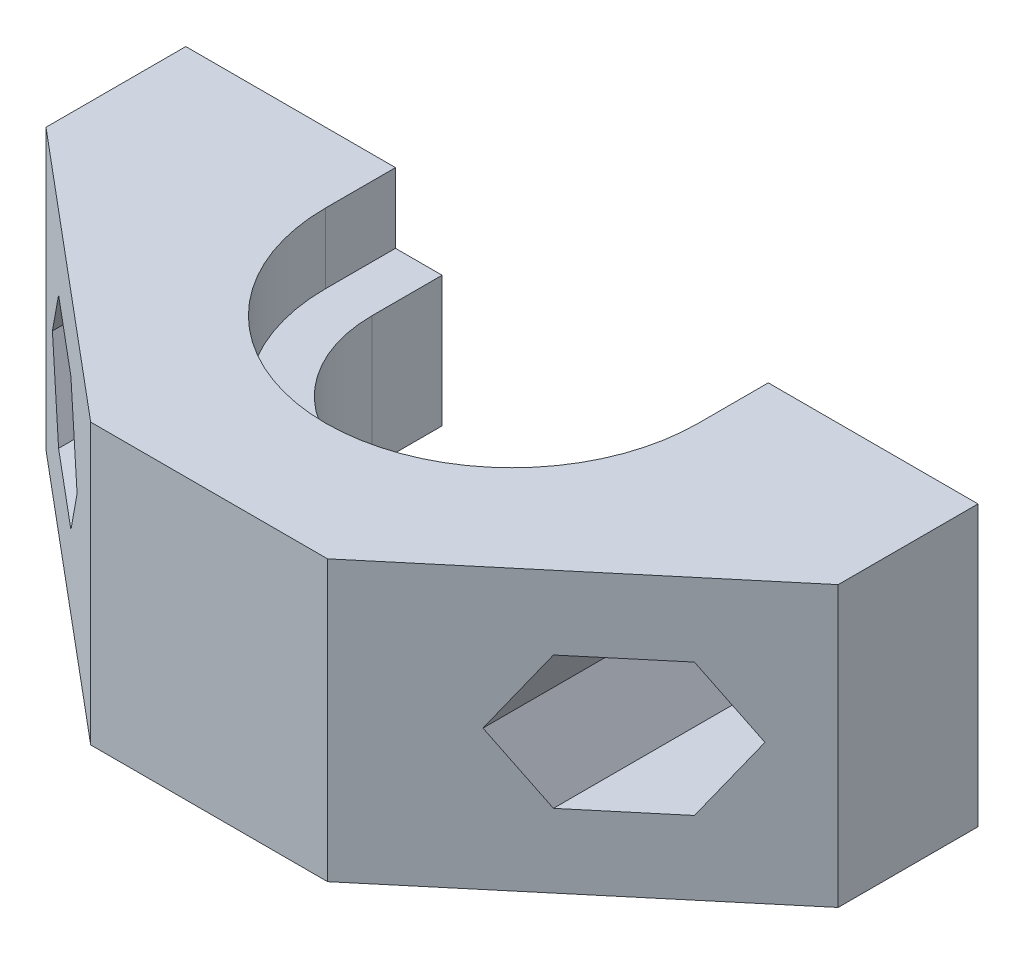
SolidWorks part; units mm, degrees
ref_plane "前视基准面" through (0, 0, 0) normal (0, 0, 1) x (1, 0, 0)
ref_plane "上视基准面" through (0, 0, 0) normal (0, 1, 0) x (1, 0, 0)
ref_plane "右视基准面" through (0, 0, 0) normal (1, 0, 0) x (0, 0, -1)
sketch "草图1" plane through (0, 0, 0) normal (0, 1, 0) x (1, 0, 0)
  line L2 (-17, -3) -> (-5.0825, -13)
  line L3 (-5.0825, -13) -> (5.0825, -13)
  line L4 (5.0825, -13) -> (17, -3)
  line L5 (17, -3) -> (17, 0)
  line L6 (0, 0) -> (0, 11.7213) construction
  line L7 (8, 0) -> (7.9845, 0)
  line L9 (-17, 3) -> (-8, 3)
  line L10 (-8, 3) -> (-8, 0)
  line L12 (17, 0) -> (17, 3)
  line L13 (17, 3) -> (7.9845, 3)
  line L14 (7.9845, 3) -> (7.9845, 0)
  line L17 (0, 0) -> (-32.6712, 0) construction
  line L18 (-17, -3) -> (-17, 3)
  arc A0 (-8, 0) -> (8, 0) centre (0, 0) ccw
  dimension "D1" = 16
  dimension "D2" = 3
  dimension "D3" = 17
  dimension "D4" = 3
  dimension "D5" = 17
  dimension "D7" = 140
  dimension "D8" = 140
  dimension "D11" = 3
extrude "凸台-拉伸1" add sketch "草图1" along normal blind 3.4
sketch "草图2" plane through (0, 3.4, 0) normal (0, 1, 0) x (1, 0, 0)
  line L8 (-8, 0) -> (-8, 3)
  line L9 (-17, -3) -> (-5.0825, -13)
  line L10 (-5.0825, -13) -> (5.0825, -13)
  line L11 (5.0825, -13) -> (17, -3)
  line L12 (17, -3) -> (17, 3)
  line L13 (7.9845, 0) -> (8, 0)
  line L16 (-17, -3) -> (-5.0825, -13)
  line L17 (-5.0825, -13) -> (5.0825, -13)
  line L18 (5.0825, -13) -> (17, -3)
  line L19 (17, -3) -> (17, 3)
  line L25 (-6, 0) -> (-6, 3)
  line L26 (-8, 3) -> (-17, 3)
  line L27 (-6, 3) -> (-17, 3)
  line L28 (-17, 3) -> (-17, -3)
  line L29 (-17, 3) -> (-17, -3)
  line L30 (17, 3) -> (7.9845, 3)
  line L31 (17, 3) -> (6, 3)
  line L32 (7.9845, 3) -> (7.9845, 0)
  line L33 (6, 3) -> (6, 0)
  arc A0 (-6, 0) -> (6, 0) centre (0, 0) ccw
  arc A1 (-8, 0) -> (8, 0) centre (0, 0) ccw
  dimension "D2" = 12
  dimension "D1" = 0
extrude "凸台-拉伸2" add sketch "草图2" along normal blind 5.6
sketch "草图3" plane through (0, 9, 0) normal (0, 1, 0) x (1, 0, 0)
  line L8 (-6, 0) -> (-6, 3)
  line L9 (-17, -3) -> (-5.0825, -13)
  line L10 (-5.0825, -13) -> (5.0825, -13)
  line L11 (5.0825, -13) -> (17, -3)
  line L12 (17, -3) -> (17, 3)
  line L16 (-17, -3) -> (-5.0825, -13)
  line L17 (-5.0825, -13) -> (5.0825, -13)
  line L18 (5.0825, -13) -> (17, -3)
  line L19 (17, -3) -> (17, 3)
  line L25 (-8, 0) -> (-8, 3)
  line L26 (-6, 3) -> (-17, 3)
  line L27 (-8, 3) -> (-17, 3)
  line L28 (-17, 3) -> (-17, -3)
  line L29 (-17, 3) -> (-17, -3)
  line L30 (17, 3) -> (6, 3)
  line L31 (17, 3) -> (8, 3)
  line L32 (6, 3) -> (6, 0)
  line L33 (8, 3) -> (8, 0)
  arc A0 (-8, 0) -> (8, 0) centre (0, 0) ccw construction
  arc A1 (-6, 0) -> (6, 0) centre (0, 0) ccw
  arc A3 (-8, 0) -> (8, 0) centre (0, 0) ccw
  dimension "D1" = 0
extrude "凸台-拉伸3" add sketch "草图3" along normal blind 3
ref_plane "基准面1" through (0, 0, 0) normal (0, 0, -1) x (-1, 0, 0)
sketch "草图5" plane through (0, 0, 0) normal (0, 0, -1) x (-1, 0, 0)
  line L1 (-17, 12) -> (-17, 0) construction
  line L2 (-5.0825, 0) -> (-17, 0) construction
  line L3 (17, 0) -> (5.0825, 0) construction
  line L4 (17, 12) -> (17, 0) construction
  circle A0 centre (12, 6) radius 1.65
  circle A1 centre (-12, 6) radius 1.65
  dimension "D1" = 3.3
  dimension "D2" = 3.3
  dimension "D3" = 5
  dimension "D4" = 5
  dimension "D5" = 6
  dimension "D6" = 6
extrude "切除-拉伸2" cut sketch "草图5" along normal through all both and the other way through all
sketch "草图4" plane through (0, 0, 0) normal (0, 0, -1) x (-1, 0, 0)
  line L16 (17, 0) -> (5.0825, 0) construction
  line L17 (10.3546, 3.15) -> (13.6454, 3.15)
  line L18 (13.6454, 3.15) -> (15.2909, 6)
  line L19 (15.2909, 6) -> (13.6454, 8.85)
  line L20 (13.6454, 8.85) -> (10.3546, 8.85)
  line L21 (10.3546, 8.85) -> (8.7091, 6)
  line L22 (8.7091, 6) -> (10.3546, 3.15)
  line L23 (-13.6454, 3.15) -> (-10.3546, 3.15)
  line L24 (-10.3546, 3.15) -> (-8.7091, 6)
  line L25 (-8.7091, 6) -> (-10.3546, 8.85)
  line L26 (-10.3546, 8.85) -> (-13.6454, 8.85)
  line L27 (-13.6454, 8.85) -> (-15.2909, 6)
  line L28 (-15.2909, 6) -> (-13.6454, 3.15)
  line L29 (-5.0825, 0) -> (-17, 0) construction
  circle A0 centre (12, 6) radius 2.85 construction
  circle A1 centre (-12, 6) radius 2.85 construction
  dimension "D1" = 5.7
  dimension "D2" = 5.7
extrude "切除-拉伸1" cut sketch "草图4" against normal up to next
